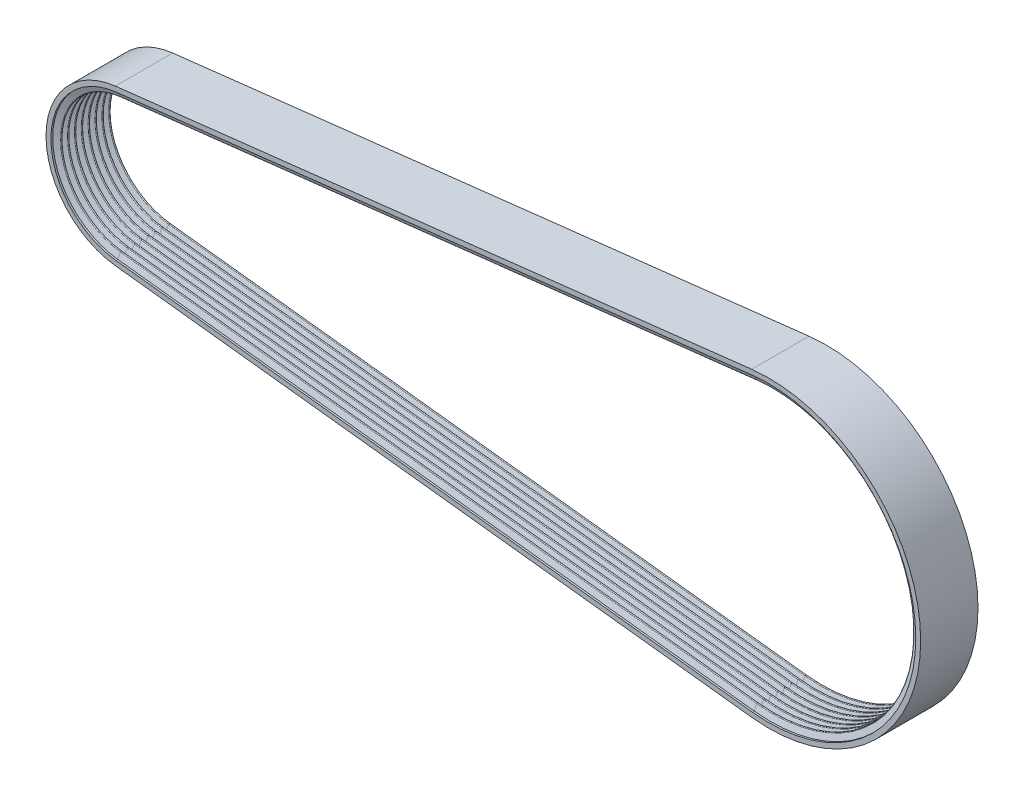
SolidWorks part; units mm, degrees
material "Rubber"
ref_plane "Front Plane" through (0, 0, 0) normal (0, 0, 1) x (1, 0, 0)
ref_plane "Top Plane" through (0, 0, 0) normal (0, 1, 0) x (1, 0, 0)
ref_plane "Right Plane" through (0, 0, 0) normal (1, 0, 0) x (0, 0, -1)
sketch "Sketch1" plane through (0, 0, 0) normal (0, 0, 1) x (1, 0, 0)
  line L0 (0, 0) -> (334.6196, 0) construction
  line L1 (55, 0) -> (-55, 0) construction
  line L2 (-4.3381, 37.8522) -> (325.9434, 75.7045)
  line L3 (325.9434, -75.7045) -> (-4.3381, -37.8522)
  arc A0 (-4.3381, 37.8522) -> (-4.3381, -37.8522) centre (0, 0) ccw
  arc A1 (325.9434, 75.7045) -> (325.9434, -75.7045) centre (334.6196, 0) cw
  dimension "D2" = 38.1
  dimension "D3" = 76.2
  dimension "D1" = 334.6196
ref_plane "Plane1" through (-4.3381, 37.8522, 0) normal (0.9935, 0.1139, 0) x (0, 0, -1)
sketch "Sketch2" plane through (-4.3381, 37.8522, 0) normal (0.9935, 0.1139, 0) x (0, 0, -1)
  line L0 (0, 0) -> (0, -3.2869) construction
  line L1 (0, 2.54) -> (14.8794, 2.54)
  line L2 (0, 2.54) -> (0, 0.2507)
  line L3 (14.8794, 2.54) -> (14.8794, 0)
  line L4 (13.9269, 0) -> (14.8794, 0)
  line L6 (0.358, 0) -> (-0.358, 0) construction
  line L7 (3.5712, -0.1303) -> (0, -0.1303) construction
  line L8 (0, -0.1303) -> (0, 0) construction
  line L9 (0, 0) -> (0, 0.2507) construction
  line L14 (12.1413, -2.9386) -> (9.2861, -2.9386) construction
  line L15 (8.5701, -2.9386) -> (5.7149, -2.9386) construction
  line L16 (4.9988, -2.9386) -> (2.1436, -2.9386) construction
  line L18 (0.358, 0) -> (3.2132, 0) construction
  line L19 (0.358, 0) -> (1.4276, -2.9386)
  line L20 (3.2132, 0) -> (3.9293, 0) construction
  line L21 (2.1436, -2.9386) -> (3.2132, 0)
  line L22 (3.9293, 0) -> (6.7845, 0) construction
  line L23 (3.9293, 0) -> (4.9988, -2.9386)
  line L24 (6.7845, 0) -> (7.5005, 0) construction
  line L25 (5.7149, -2.9386) -> (6.7845, 0)
  line L26 (7.5005, 0) -> (10.3557, 0) construction
  line L27 (7.5005, 0) -> (8.5701, -2.9386)
  line L28 (11.0717, 0) -> (13.9269, 0) construction
  line L29 (9.2861, -2.9386) -> (10.3557, 0)
  line L31 (11.0717, 0) -> (12.1413, -2.9386)
  line L33 (12.8574, -2.9386) -> (13.9269, 0)
  arc A0 (12.1413, -2.9386) -> (12.8574, -2.9386) centre (12.4993, -2.8083) ccw
  arc A1 (11.0717, 0) -> (10.3557, 0) centre (10.7137, -0.1303) ccw
  arc A2 (8.5701, -2.9386) -> (9.2861, -2.9386) centre (8.9281, -2.8083) ccw
  arc A3 (4.9988, -2.9386) -> (5.7149, -2.9386) centre (5.3569, -2.8083) ccw
  arc A4 (1.4276, -2.9386) -> (2.1436, -2.9386) centre (1.7856, -2.8083) ccw
  arc A5 (0.358, 0) -> (0, 0.2507) centre (0, -0.1303) ccw
  arc A13 (3.9293, 0) -> (3.2132, 0) centre (3.5712, -0.1303) ccw
  arc A14 (7.5005, 0) -> (6.7845, 0) centre (7.1425, -0.1303) ccw
  dimension "D6" = 2.54
  dimension "D2" = 0.381
  dimension "D1" = 0.9525
  dimension "D3" = 3.5712
  dimension "D4" = 20
sweep "Sweep1" add profiles "Sketch2" path "Sketch1"
mirror "Mirror1" of "Sweep1"
